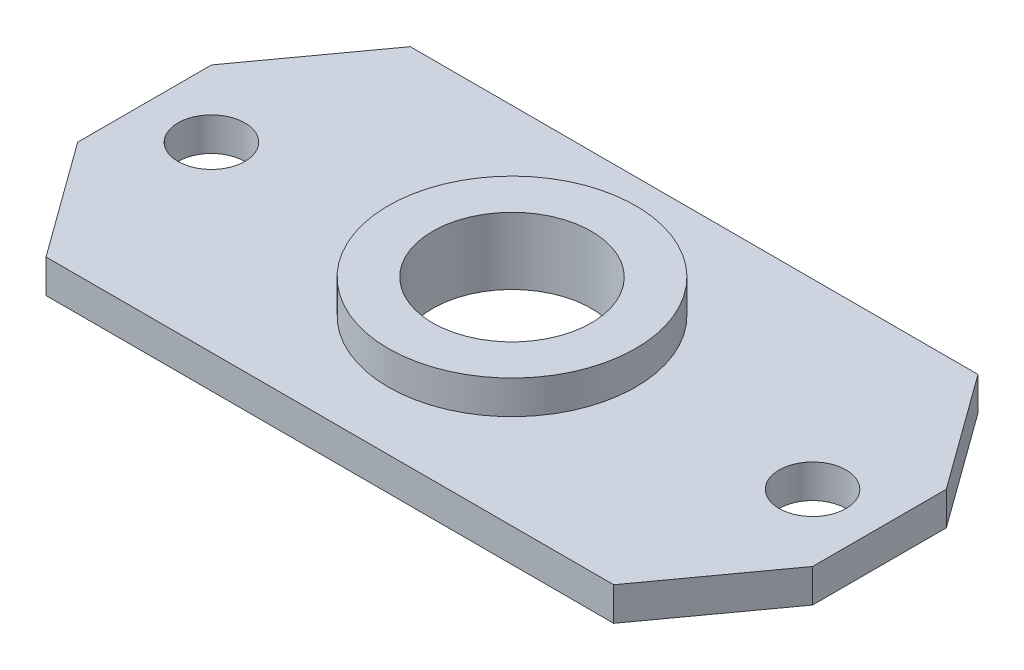
SolidWorks part; units mm, degrees
ref_plane "Front Plane" through (0, 0, 0) normal (0, 0, 1) x (1, 0, 0)
ref_plane "Top Plane" through (0, 0, 0) normal (0, 1, 0) x (1, 0, 0)
ref_plane "Right Plane" through (0, 0, 0) normal (1, 0, 0) x (0, 0, -1)
sketch "Sketch1" plane through (0, 0, 0) normal (0, 1, 0) x (1, 0, 0)
  line L0 (16.98, 21.79) -> (16.98, 0) construction
  line L1 (0, 0) -> (33.96, 0)
  line L3 (0, 21.79) -> (33.96, 21.79)
  line L5 (-5, 10.895) -> (38.96, 10.895) construction
  line L6 (0, 21.79) -> (-5, 14.895)
  line L7 (-5, 14.895) -> (-5, 6.895)
  line L8 (-5, 6.895) -> (0, 0)
  line L9 (33.96, 21.79) -> (38.96, 14.895)
  line L10 (38.96, 14.895) -> (38.96, 6.895)
  line L11 (38.96, 6.895) -> (33.96, 0)
  circle A0 centre (-1, 10.895) radius 2
  circle A1 centre (34.96, 10.895) radius 2
  circle A2 centre (-1, 10.895) radius 2
  circle A3 centre (34.96, 10.895) radius 2
  point P19 (16.98, 10.895)
  dimension "D5" = 4
  dimension "D1" = 33.96
  dimension "D2" = 21.79
  dimension "D3" = 8
  dimension "D4" = 5
  dimension "D6" = 21.79
  dimension "D7" = 4
extrude "Boss-Extrude1" add sketch "Sketch1" along normal blind 2
sketch "Sketch2" plane through (0, 2, 0) normal (0, 1, 0) x (1, 0, 0)
  line L0 (-5, 10.895) -> (38.96, 10.895) construction
  line L3 (38.96, 14.895) -> (38.96, 6.895) construction
  line L6 (-5, 14.895) -> (-5, 6.895) construction
  circle A0 centre (16.98, 10.895) radius 7.4
  dimension "D1" = 14.8
extrude "Boss-Extrude2" add sketch "Sketch2" along normal blind 2
sketch "Sketch3" plane through (0, 4, 0) normal (0, 1, 0) x (1, 0, 0)
  circle A0 centre (16.98, 10.895) radius 4.75
  dimension "D1" = 9.5
extrude "Cut-Extrude1" cut sketch "Sketch3" against normal through all
equation "\"8mm hole\" = 8.4mm"
equation "\"22mm hole\"= 23mm"
equation "\"15mm hole\"= 15.8mm"
equation "\"bed height offset\"= 3mm"
equation "\"D1@Sketch2\"=\"15mm hole\" - 1"
